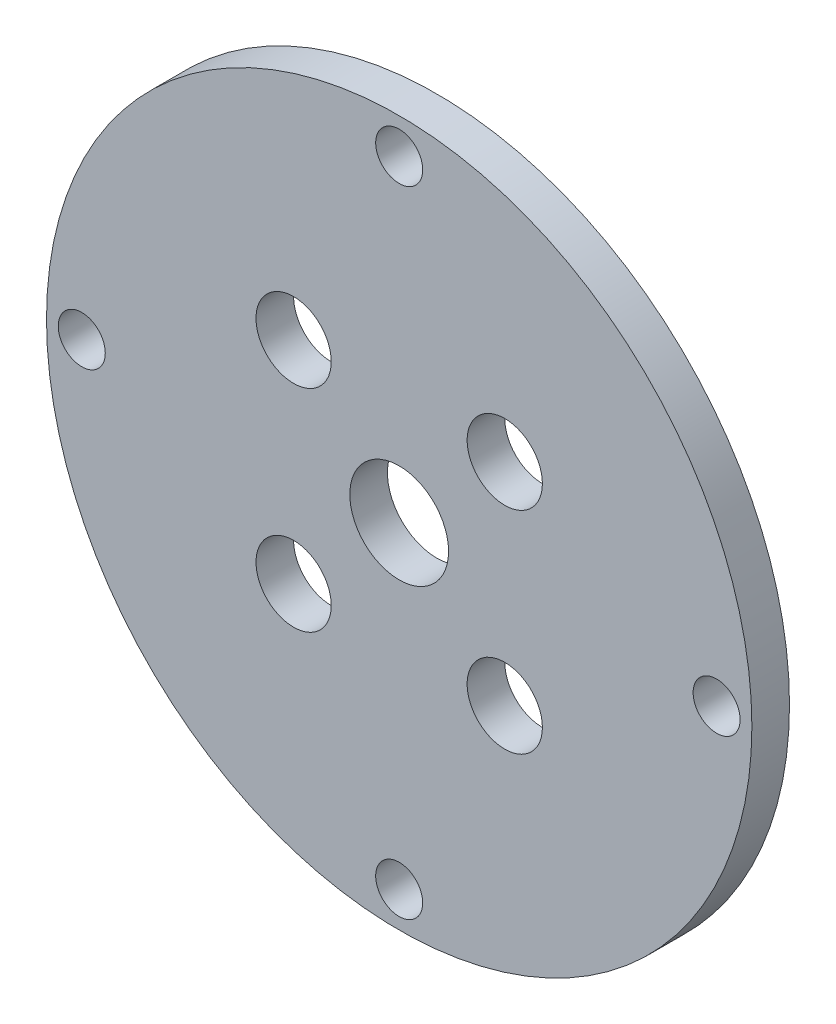
SolidWorks part; units mm, degrees
ref_plane "Front" through (0, 0, 0) normal (0, 0, 1) x (1, 0, 0)
ref_plane "Top" through (0, 0, 0) normal (0, 1, 0) x (1, 0, 0)
ref_plane "Right" through (0, 0, 0) normal (1, 0, 0) x (0, 0, -1)
sketch "Sketch1" plane through (0, 0, 0) normal (0, 0, 1) x (1, 0, 0)
  circle A0 centre (0, 0) radius 15
  circle A2 centre (0, 0) radius 2.1
  circle A3 centre (4.4901, 4.4901) radius 1.6
  circle A4 centre (4.4901, -4.4901) radius 1.6
  circle A5 centre (-4.4901, -4.4901) radius 1.6
  circle A6 centre (-4.4901, 4.4901) radius 1.6
  circle A7 centre (0, 13.5) radius 1
  circle A8 centre (13.5, 0) radius 1
  circle A9 centre (0, -13.5) radius 1
  circle A10 centre (-13.5, 0) radius 1
  dimension "D1" = 4
  dimension "D2" = 4
extrude "Boss-Extrude1" add sketch "Sketch1" along normal blind 1.6
